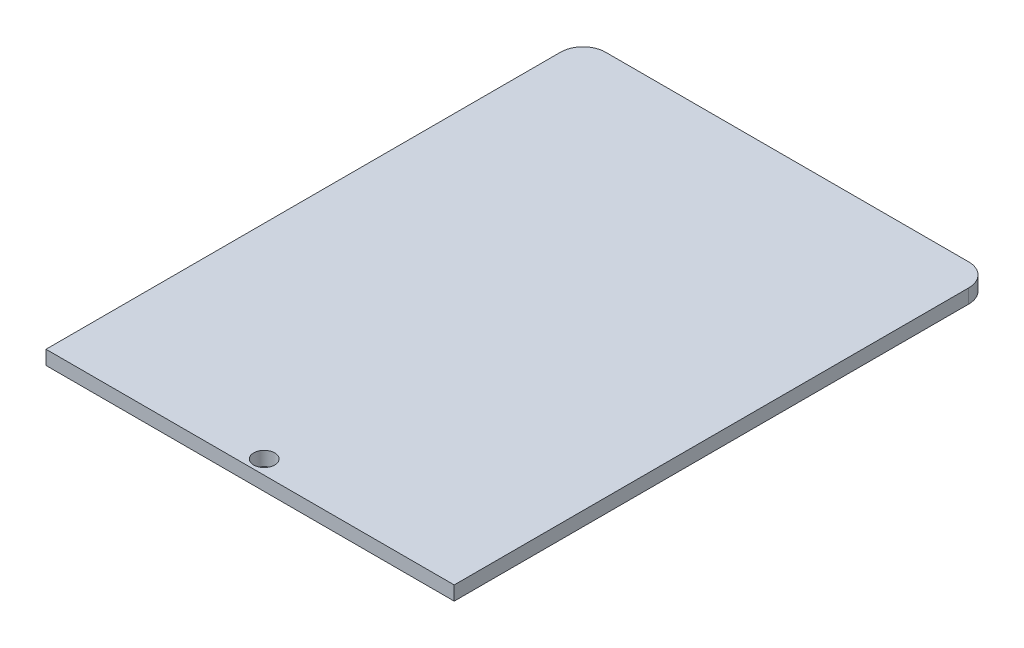
SolidWorks part; units mm, degrees
ref_plane "Front Plane" through (0, 0, 0) normal (0, 0, 1) x (1, 0, 0)
ref_plane "Top Plane" through (0, 0, 0) normal (0, 1, 0) x (1, 0, 0)
ref_plane "Right Plane" through (0, 0, 0) normal (1, 0, 0) x (0, 0, -1)
sketch "Sketch1" plane through (0, 0, 0) normal (0, 1, 0) x (1, 0, 0)
  line L0 (2.54, 60.579) -> (43.5063, 60.579)
  line L1 (0, 58.039) -> (0, 0)
  line L2 (0, 0) -> (46.0463, 0)
  line L3 (46.0463, 58.039) -> (46.0463, 0)
  circle A0 centre (23.0231, 1.5875) radius 1.1906
  arc A1 (46.0463, 58.039) -> (43.5063, 60.579) centre (43.5063, 58.039) ccw
  arc A2 (2.54, 60.579) -> (0, 58.039) centre (2.54, 58.039) ccw
  dimension "D1" = 2.54
extrude "Boss-Extrude1" add sketch "Sketch1" along normal blind 1.5875
